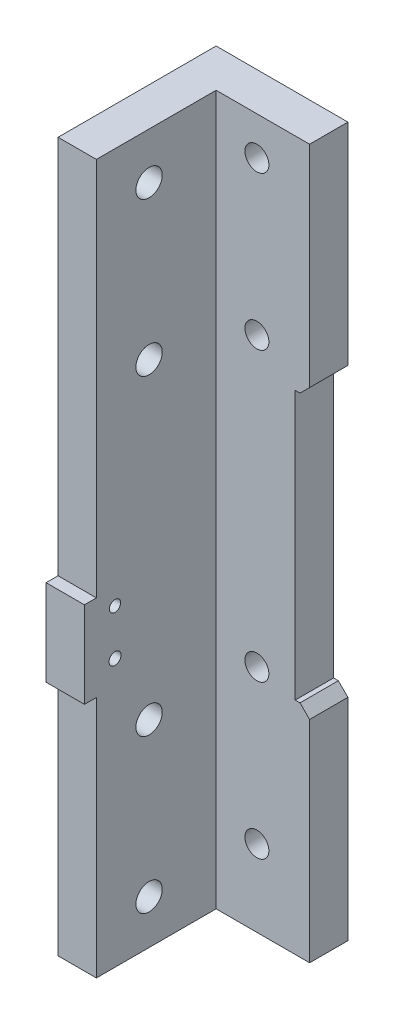
SolidWorks part; units mm, degrees
ref_plane "Plan de face" through (0, 0, 0) normal (0, 0, 1) x (1, 0, 0)
ref_plane "Plan de dessus" through (0, 0, 0) normal (0, 1, 0) x (1, 0, 0)
ref_plane "Plan de droite" through (0, 0, 0) normal (1, 0, 0) x (0, 0, -1)
sketch "Sketch1" plane through (0, 0, 0) normal (0, 0, 1) x (1, 0, 0)
  line L1 (0, 0) -> (-24.51, 0)
  line L2 (0, 0) -> (0, 148)
  line L3 (0, 148) -> (-24.51, 148)
  line L4 (-24.51, 0) -> (-24.51, 148)
  dimension "D1" = 24.51
  dimension "D2" = 148
extrude "Boss-Extrude1" add sketch "Sketch1" along normal blind 8
sketch "Sketch2" plane through (0, 0, 8) normal (0, 0, 1) x (1, 0, 0)
  line L0 (-24.51, 0) -> (0, 0) construction
  line L1 (-24.51, 148) -> (-16.51, 148)
  line L2 (-24.51, 148) -> (-24.51, 0)
  line L3 (-24.51, 0) -> (-16.51, 0)
  line L4 (-16.51, 148) -> (-16.51, 0)
  dimension "D1" = 8
extrude "Boss-Extrude2" add sketch "Sketch2" along normal blind 25
sketch "Sketch3" plane through (0, 0, 8) normal (0, 0, 1) x (1, 0, 0)
  line L1 (0, 0) -> (0, 148) construction
  line L5 (0, 148) -> (-16.51, 148) construction
  circle A0 centre (-8, 16) radius 2.5
  circle A1 centre (-8, 48) radius 2.5
  circle A2 centre (-8, 108) radius 2.5
  circle A3 centre (-8, 140) radius 2.5
  dimension "D1" = 5
  dimension "D2" = 5
  dimension "D8" = 5
  dimension "D9" = 5
  dimension "D3" = 32
  dimension "D4" = 8
  dimension "D5" = 8
  dimension "D6" = 60
  dimension "D7" = 32
extrude "Cut-Extrude1" cut sketch "Sketch3" against normal blind 10
sketch "Sketch4" plane through (-24.51, 0, 0) normal (-1, 0, 0) x (0, 0, 1)
  line L0 (33, 148) -> (33, 0) construction
  line L1 (33, 148) -> (0, 148) construction
  circle A0 centre (22, 138.3) radius 2.75
  circle A1 centre (22, 106.3) radius 2.75
  circle A2 centre (22, 41.2) radius 2.75
  circle A3 centre (22, 9.2) radius 2.75
  dimension "D1" = 5.5
  dimension "D5" = 5.5
  dimension "D7" = 5.5
  dimension "D8" = 5.5
  dimension "D2" = 11
  dimension "D3" = 9.7
  dimension "D4" = 32
  dimension "D6" = 11
  dimension "D9" = 65.1
  dimension "D10" = 32
  dimension "D11" = 11
  dimension "D12" = 11
extrude "Cut-Extrude2" cut sketch "Sketch4" against normal up to surface (8 mm away) up to face at (-16.51, 55.5, 26.75)
sketch "Sketch5" plane through (0, 0, 0) normal (0, 0, -1) x (-1, 0, 0)
  line L1 (0, 148) -> (-3, 148)
  line L2 (0, 148) -> (0, 102)
  line L3 (0, 102) -> (-3, 102)
  line L4 (-3, 148) -> (-3, 102)
  dimension "D1" = 46
  dimension "D2" = 3
extrude "Boss-Extrude3" add sketch "Sketch5" against normal up to surface (8 mm away) up to face at (-10.5, 140, 8)
sketch "Sketch6" plane through (0, 0, 0) normal (0, 0, -1) x (-1, 0, 0)
  line L1 (0, 0) -> (-3, 0)
  line L2 (0, 0) -> (0, 46)
  line L3 (0, 46) -> (-3, 46)
  line L4 (-3, 0) -> (-3, 46)
  dimension "D1" = 3
  dimension "D2" = 46
extrude "Boss-Extrude4" add sketch "Sketch6" against normal up to surface (8 mm away) up to face at (-10.5, 140, 8)
chamfer "Chamfer1" distance 2 angle 45 2 edges at (3, 46, 4) (3, 102, 4)
sketch "Sketch7" plane through (-24.51, 0, 0) normal (-1, 0, 0) x (0, 0, 1)
  line L0 (33, 148) -> (33, 0) construction
  line L1 (29.5, 50.7222) -> (35.5, 50.7222)
  line L2 (29.5, 50.7222) -> (29.5, 68.7222)
  line L3 (29.5, 68.7222) -> (35.5, 68.7222)
  line L4 (35.5, 50.7222) -> (35.5, 68.7222)
  dimension "D1" = 2.5
  dimension "D2" = 18
  dimension "D3" = 6
extrude "Boss-Extrude5" add sketch "Sketch7" against normal up to surface (8 mm away) up to face at (-16.51, 6.45, 22)
sketch "Sketch8" plane through (-24.51, 0, 0) normal (-1, 0, 0) x (0, 0, 1)
  circle A0 centre (29.1121, 65.3222) radius 1.175
  circle A1 centre (29.1121, 55.8222) radius 1.25
extrude "Cut-Extrude3" cut sketch "Sketch8" against normal up to surface (8 mm away) up to face at (-16.51, 6.45, 22)
equation "\"D9@Sketch3\"=\"D8@Sketch3\""
